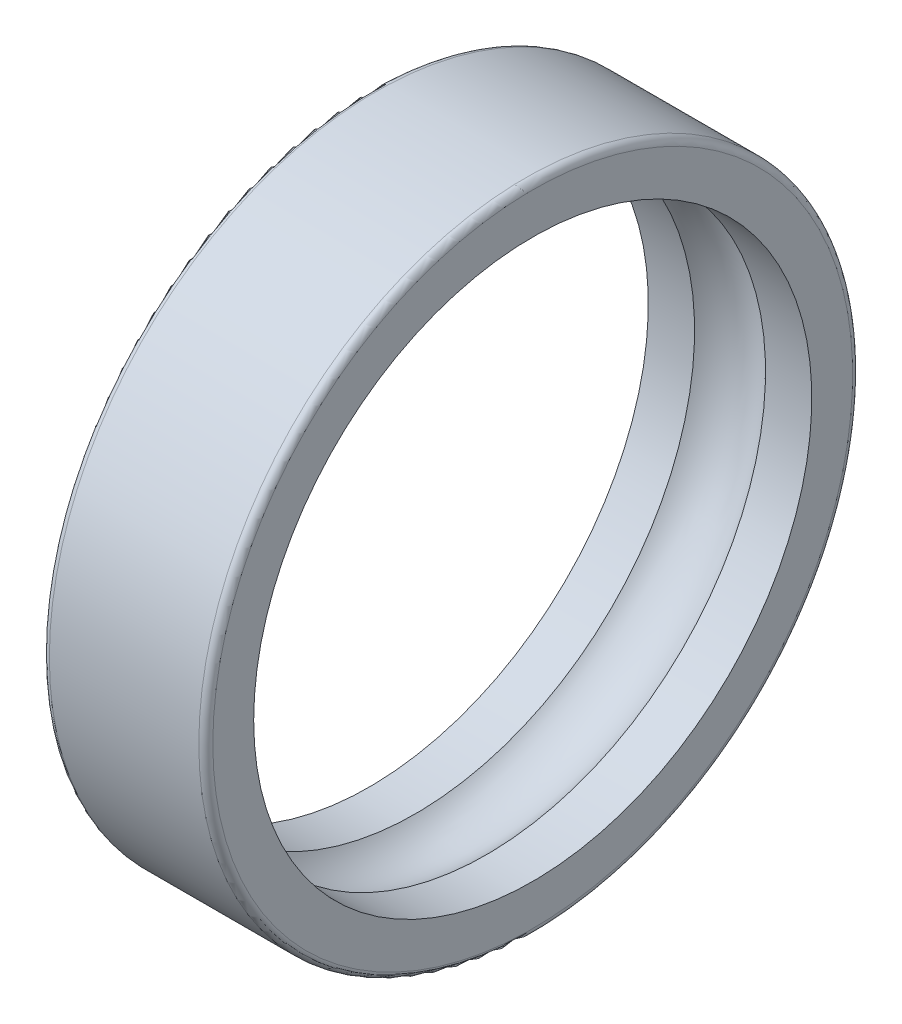
SolidWorks part; units mm, degrees
ref_plane "Front Plane" through (0, 0, 0) normal (0, 0, 1) x (1, 0, 0)
ref_plane "Top Plane" through (0, 0, 0) normal (0, 1, 0) x (1, 0, 0)
ref_plane "Right Plane" through (0, 0, 0) normal (1, 0, 0) x (0, 0, -1)
ref_plane "Plane1" through (0, 0, 0) normal (0, 0, 1) x (1, 0, 0)
sketch "Sketch1" plane through (0, 0, 0) normal (0, 0, 1) x (1, 0, 0)
  line L0 (0, 6.85) -> (0, 5.975)
  line L1 (0, 5.975) -> (0.9905, 5.975)
  line L2 (2.5095, 5.975) -> (3.5, 5.975)
  line L3 (3.5, 5.975) -> (3.5, 6.85)
  line L4 (3.35, 7) -> (0.15, 7)
  line L5 (3.5, 0) -> (0, 0) construction
  arc A0 (0.9905, 5.975) -> (2.5095, 5.975) centre (1.75, 5.25) cw
  arc A1 (3.5, 6.85) -> (3.35, 7) centre (3.35, 6.85) ccw
  arc A2 (0.15, 7) -> (0, 6.85) centre (0.15, 6.85) ccw
revolve "Revolve1" add sketch "Sketch1" angle 360 about L5
